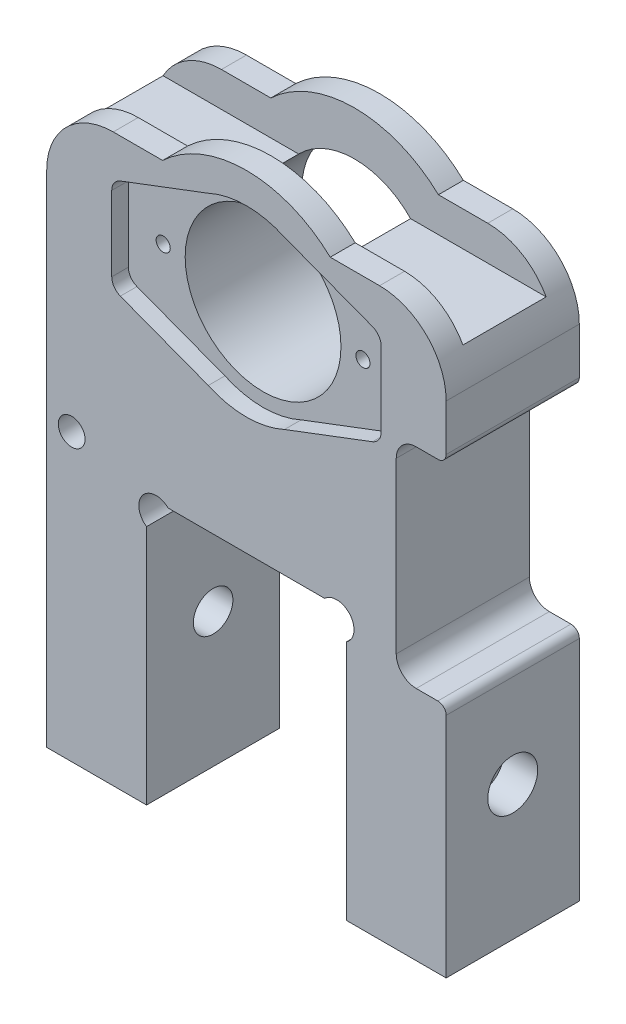
SolidWorks part; units mm, degrees
ref_plane "Front Plane" through (0, 0, 0) normal (0, 0, 1) x (1, 0, 0)
ref_plane "Top Plane" through (0, 0, 0) normal (0, 1, 0) x (1, 0, 0)
ref_plane "Right Plane" through (0, 0, 0) normal (1, 0, 0) x (0, 0, -1)
sketch "Sketch1" plane through (0, 0, 0) normal (0, 0, 1) x (1, 0, 0)
  line L0 (0, 0) -> (0, -31.549) construction
  line L1 (38.1, -57.15) -> (19.05, -57.15)
  line L2 (38.1, -57.15) -> (38.1, 50.8697)
  line L4 (-38.1, -57.15) -> (-38.1, 50.8697)
  line L5 (38.1, -57.15) -> (-38.1, 57.15) construction
  line L6 (38.1, 57.15) -> (-38.1, -57.15) construction
  line L8 (19.05, -57.15) -> (19.05, -11.1547)
  line L9 (14.9316, -6.0263) -> (-14.9316, -6.0263)
  line L10 (-19.05, -57.15) -> (-19.05, -11.1547)
  line L11 (19.05, -57.15) -> (-19.05, -5.948) construction
  line L12 (19.05, -6.096) -> (-19.05, -57.15) construction
  line L13 (-19.05, -57.15) -> (-38.1, -57.15)
  line L16 (-26.721, 19.0689) -> (28.5427, 19.0689) construction
  line L17 (0, 33.9279) -> (0, 0) construction
  line L18 (-38.1, 50.8697) -> (-15.9838, 50.8697)
  line L19 (15.9838, 50.8697) -> (38.1, 50.8697)
  line L20 (-33.3375, -57.15) -> (-33.3375, -2.6115) construction
  line L21 (19.05, -11.1547) -> (19.05, -6.096) construction
  line L22 (19.05, -6.096) -> (-19.05, -5.948) construction
  circle A0 centre (0, 33.9279) radius 14.859
  arc A1 (-14.9316, -6.0263) -> (-19.05, -11.1547) centre (-17.2217, -8.405) ccw
  arc A2 (14.9316, -6.0263) -> (19.05, -11.1547) centre (17.2217, -8.405) cw
  arc A3 (15.9838, 50.8697) -> (-15.9838, 50.8697) centre (0, 33.9279) ccw
  circle A4 centre (-33.3375, -2.6115) radius 2.5527
  circle A5 centre (33.3375, -2.6115) radius 2.5527
  point P0 (0, 0)
  point P6 (0.0276, -31.5861)
  dimension "D4" = 29.718
  dimension "D9" = 5.1054
  dimension "D15" = 3.302
  dimension "D1" = 76.2
  dimension "D3" = 51.054
  dimension "D6" = 114.3
  dimension "D7" = 39.9542
  dimension "D8" = 3.0626
  dimension "D12" = 45.9953
  dimension "D13" = 45.9953
  dimension "D16" = 4.7625
extrude "Boss-Extrude1" add sketch "Sketch1" along normal blind 25.4
fillet "Fillet1" radius 12.7 2 edges at (-38.1, 50.8697, 12.7) (38.1, 50.8697, 12.7)
sketch "Sketch2" plane through (0, 0, 25.4) normal (0, 0, 1) x (1, 0, 0)
  line L0 (-10.6948, 33.9279) -> (12.1563, 33.9279) construction
  line L2 (25.6921, 25.0379) -> (25.6921, 42.8179)
  line L4 (-25.6921, 25.0379) -> (-25.6921, 42.8179)
  line L5 (25.6921, 25.0379) -> (-25.6921, 42.8179) construction
  line L6 (25.6921, 42.8179) -> (-25.6921, 25.0379) construction
  line L7 (-7.2748, 49.8029) -> (7.2748, 49.8029) construction
  line L8 (-11.2908, 51.3904) -> (10.6771, 51.3904) construction
  line L9 (-25.6921, 42.8179) -> (-7.2748, 49.8029)
  line L10 (7.2748, 49.8029) -> (25.6921, 42.8179)
  line L11 (-25.6921, 25.0379) -> (-7.2748, 18.0529)
  line L12 (7.2748, 18.0529) -> (25.6921, 25.0379)
  arc A0 (-7.2748, 18.0529) -> (7.2748, 18.0529) centre (0, 33.9279) ccw
  arc A1 (7.2748, 49.8029) -> (-7.2748, 49.8029) centre (0, 33.9279) ccw
  dimension "D1" = 34.925
  dimension "D5" = 17.4625
  dimension "D2" = 51.3842
  dimension "D3" = 17.78
  dimension "D4" = 1.5875
extrude "Cut-Extrude1" cut sketch "Sketch2" against normal blind 3.175
fillet "Fillet2" radius 2.54 4 edges at (-25.6921, 25.0379, 23.8125) (-25.6921, 42.8179, 23.8125) (25.6921, 25.0379, 23.8125) (25.6921, 42.8179, 23.8125)
sketch "Sketch3" plane through (0, 0, 22.225) normal (0, 0, 1) x (1, 0, 0)
  line L0 (-19.05, 33.9279) -> (19.05, 33.9279) construction
  line L1 (0, 33.9279) -> (0, 19.0689) construction
  circle A0 centre (-19.05, 33.9279) radius 1.3462
  circle A1 centre (19.05, 33.9279) radius 1.3462
  circle A2 centre (0, 33.9279) radius 14.859 construction
  dimension "D1" = 2.6924
  dimension "D2" = 38.1
extrude "Cut-Extrude2" cut sketch "Sketch3" against normal up to vertex (22.225 mm away)
sketch "Sketch4" plane through (-38.1, 0, 0) normal (-1, 0, 0) x (0, 0, 1)
  line L0 (12.7, -57.15) -> (12.7, -31.496) construction
  line L1 (25.4, -57.15) -> (0, -57.15) construction
  circle A0 centre (12.7, -31.496) radius 3.7703
  dimension "D1" = 7.5406
  dimension "D2" = 25.654
extrude "Cut-Extrude3" cut sketch "Sketch4" against normal up to vertex
sketch "Sketch5" plane through (0, 50.8697, 0) normal (0, 1, 0) x (1, 0, 0)
  line L0 (-38.1, -12.7) -> (38.1, -12.7) construction
  line L1 (-38.1, -25.4) -> (-38.1, 0) construction
  line L2 (38.1, 0) -> (38.1, -25.4) construction
  line L3 (-38.1, -25.4) -> (38.1, -25.4) construction
  line L4 (42.9529, -4.7625) -> (-42.9529, -4.7625)
  line L5 (42.9529, -4.7625) -> (42.9529, -20.6375)
  line L6 (42.9529, -20.6375) -> (-42.9529, -20.6375)
  line L7 (-42.9529, -4.7625) -> (-42.9529, -20.6375)
  line L8 (42.9529, -4.7625) -> (-42.9529, -20.6375) construction
  line L9 (42.9529, -20.6375) -> (-42.9529, -4.7625) construction
  point P6 (0, -12.7)
  dimension "D1" = 4.7625
extrude "Cut-Extrude4" cut sketch "Sketch5" against normal blind 6.604 and the other way blind 23.622
sketch "Sketch6" plane through (0, 0, 0) normal (0, 0, -1) x (-1, 0, 0)
  line L0 (-38.1, -57.15) -> (-38.1, 38.1697) construction
  line L1 (-38.1, 27.747) -> (-28.575, 27.747)
  line L2 (-38.1, 27.747) -> (-38.1, -12.1768)
  line L3 (-38.1, -12.1768) -> (-28.575, -12.1768)
  line L4 (-28.575, 27.747) -> (-28.575, -12.1768)
  dimension "D1" = 9.525
extrude "Cut-Extrude5" cut sketch "Sketch6" against normal up to vertex
fillet "Fillet3" radius 3.81 2 edges at (28.575, -12.1768, 12.7) (28.575, 27.747, 12.7)
fillet "Fillet4" radius 1.5875 2 edges at (38.1, -12.1768, 12.7) (38.1, 27.747, 12.7)
sketch "Sketch7" plane through (38.1, 0, 0) normal (1, 0, 0) x (0, 0, -1)
  circle A0 centre (-12.7, -31.496) radius 4.7625
  dimension "D1" = 9.525
extrude "Cut-Extrude6" cut sketch "Sketch7" against normal blind 6.35
mirror "Mirror1" about plane through (0, 0, 0) normal (1, 0, 0) of "Cut-Extrude6"
